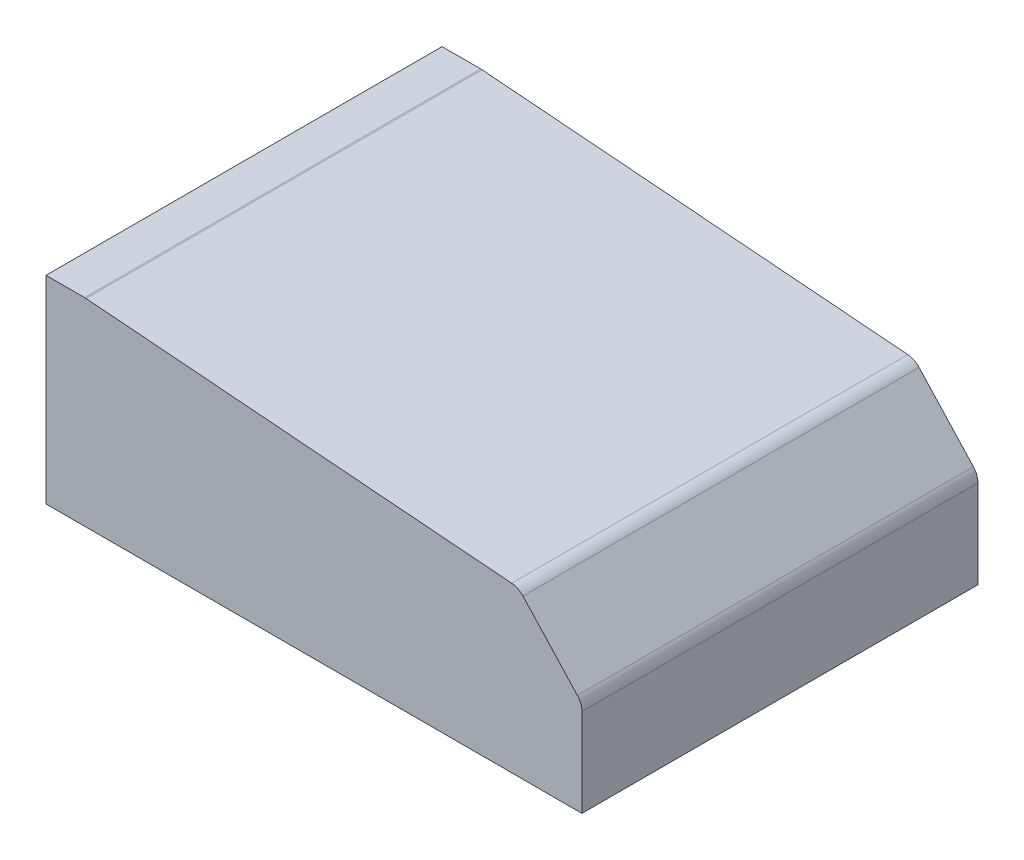
SolidWorks part; units mm, degrees
ref_plane "Front Plane" through (0, 0, 0) normal (0, 0, 1) x (1, 0, 0)
ref_plane "Top Plane" through (0, 0, 0) normal (0, 1, 0) x (1, 0, 0)
ref_plane "Right Plane" through (0, 0, 0) normal (1, 0, 0) x (0, 0, -1)
sketch "Model" plane through (0, 0, 0) normal (0, 0, 1) x (1, 0, 0)
  line L0 (0, 0) -> (0, 252)
  line L1 (682, 0) -> (0, 0)
  line L2 (682, 0) -> (682, 112.176)
  line L3 (676.1602, 127.1041) -> (607.0327, 201.9368)
  line L4 (592.6131, 208.9397) -> (50.9482, 251.931)
  line L5 (49.2076, 252) -> (0, 252)
  arc A0 (682, 112.176) -> (676.1602, 127.1041) centre (660, 112.176) ccw
  arc A1 (607.0327, 201.9368) -> (592.6131, 208.9397) centre (590.8725, 187.0086) ccw
  arc A2 (50.9482, 251.931) -> (49.2076, 252) centre (49.2076, 230) ccw
  dimension "D1" = 22
  dimension "D2" = 22
  dimension "D3" = 22
  dimension "D4" = 682
  dimension "D5" = 252
  dimension "D6" = 543.3683
  dimension "D7" = 49.2076
  dimension "D8" = 101.8751
  dimension "D9" = 112.176
extrude "Boss-Extrude1" add sketch "Model" along normal blind 504
shell "Shell1" thickness 2
